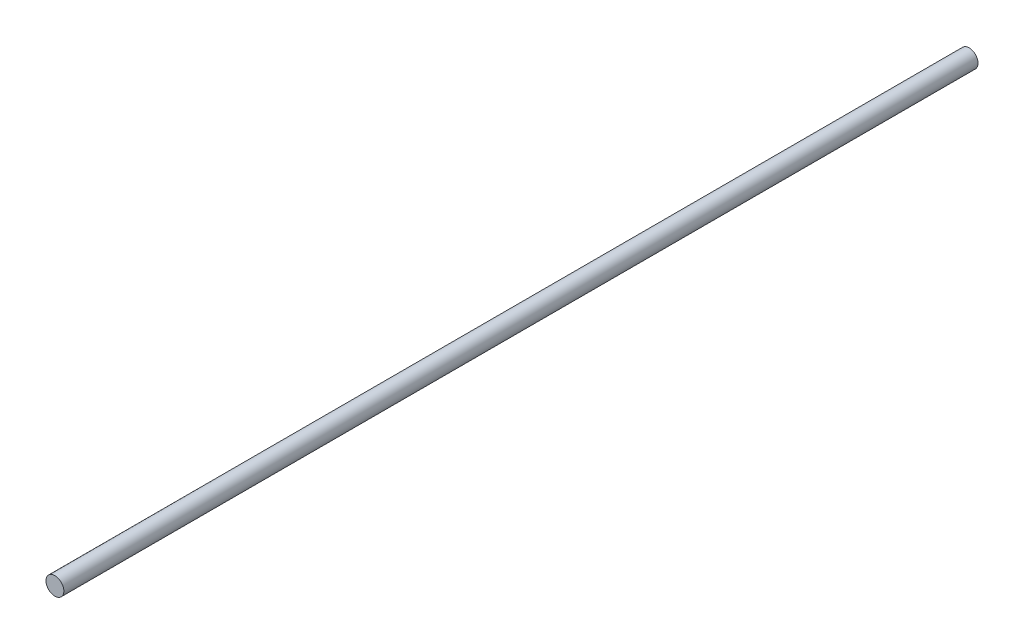
SolidWorks part; units mm, degrees
ref_plane "前视基准面" through (0, 0, 0) normal (0, 0, 1) x (1, 0, 0)
ref_plane "上视基准面" through (0, 0, 0) normal (0, 1, 0) x (1, 0, 0)
ref_plane "右视基准面" through (0, 0, 0) normal (1, 0, 0) x (0, 0, -1)
sketch "草图1" plane through (0, 0, 0) normal (0, 0, 1) x (1, 0, 0)
  circle A0 centre (0, 0) radius 4
  dimension "D1" = 8
extrude "凸台-拉伸1" add sketch "草图1" along normal blind 410
